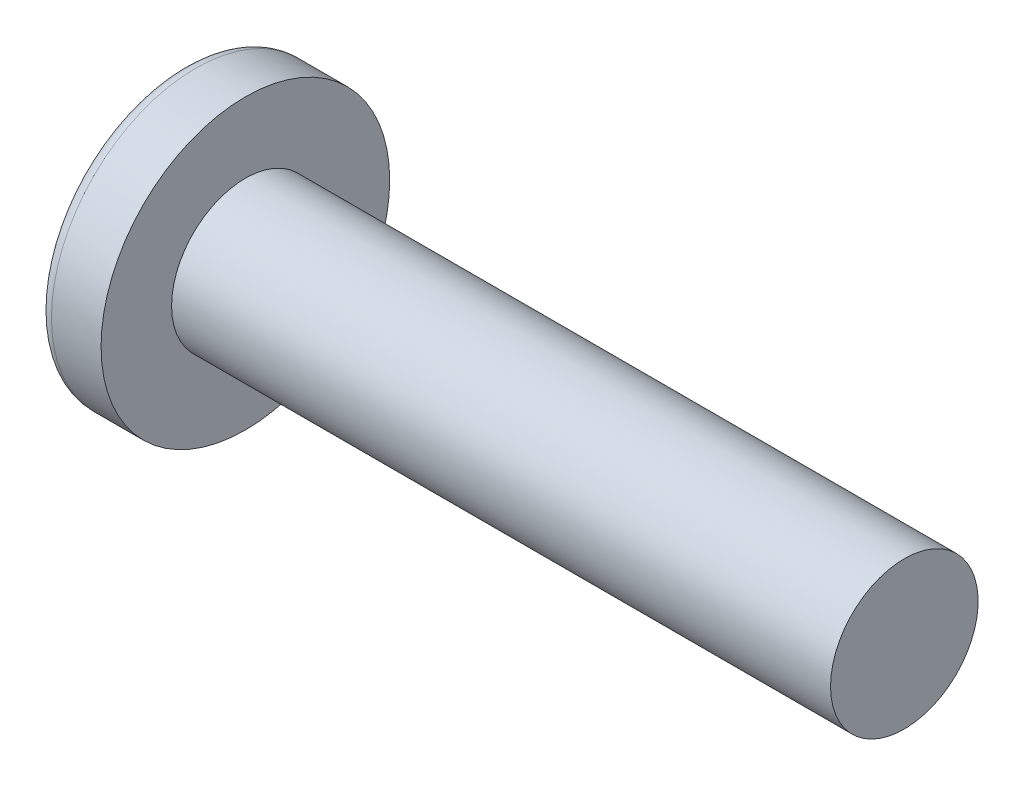
SolidWorks part; units mm, degrees
ref_plane "Plane1" through (0, 0, 0) normal (0, 0, 1) x (1, 0, 0)
ref_plane "Plane2" through (0, 0, 0) normal (0, 1, 0) x (1, 0, 0)
ref_plane "Plane3" through (0, 0, 0) normal (1, 0, 0) x (0, 0, -1)
sketch "BodySke" plane through (0, 0, 0) normal (0, 0, 1) x (1, 0, 0)
  line L0 (2.032, 1.4224) -> (2.032, 2.7813)
  line L1 (2.3495, 6.35) -> (2.3495, -3.175) construction
  line L2 (-25.4, 0) -> (127, 0) construction
  line L3 (14.732, 0) -> (0, 0)
  line L4 (2.032, 1.4224) -> (14.732, 1.4224)
  line L5 (14.732, 1.4224) -> (14.732, 0)
  line L6 (1.0756, 2.7813) -> (2.032, 2.7813)
  line L7 (2.032, -1.4224) -> (14.732, -1.4224) construction
  line L8 (2.032, 6.35) -> (2.032, -3.175) construction
  arc A0 (0.8702, 2.6767) -> (0, 0) centre (4.5517, 0) ccw
  arc A2 (0.8702, 2.6767) -> (1.0756, 2.7813) centre (1.0756, 2.5273) cw
  dimension "Head_fillet_rad" = 0.254
  dimension "Head_crown_rad" = 4.5517
  dimension "Head_ht" = 2.032
  dimension "Diameter" = 2.8448
  dimension "Length" = 12.7
  dimension "Head_dia" = 5.5626
  dimension "Advance" = 0.635
  dimension "Thread_nom" = 12.7
revolve "Base-Revolve" add sketch "BodySke" angle 360 about L2
cosmetic thread "ThreadCosmetic" [suppressed] parameters "Thread_length"=12.065, "Thread_minor"=2.0879
sketch "Sketch3" plane through (0, 0, 0) normal (1, 0, 0) x (0, 0, -1)
  line L0 (0.4064, -1.8161) -> (-0.4064, -1.8161)
  line L1 (0.4064, -1.8161) -> (0.4064, 1.8161)
  line L2 (-0.4064, 1.8161) -> (0.4064, 1.8161)
  line L3 (-0.4064, 1.8161) -> (-0.4064, -1.8161)
  dimension "D1" = 1.8161
  dimension "Cross_dia" = 3.6322
  dimension "D2" = 0.4064
  dimension "Cross_width" = 0.8128
ref_plane "Plane4" through (2.0066, 0, 0) normal (1, 0, 0) x (0, 0, -1)
sketch "Sketch4" plane through (2.0066, 0, 0) normal (1, 0, 0) x (0, 0, -1)
  line L0 (0.2032, -0.2032) -> (-0.2032, -0.2032)
  line L1 (0.2032, -0.2032) -> (0.2032, 0.2032)
  line L2 (-0.2032, 0.2032) -> (0.2032, 0.2032)
  line L3 (-0.2032, 0.2032) -> (-0.2032, -0.2032)
  dimension "D1" = 0.4064
  dimension "D2" = 0.4064
  dimension "D3" = 0.2032
  dimension "D4" = 0.2032
loft "Cut-Loft1" cut profiles "Sketch3", "Sketch4"
pattern_circular "CirPattern1" count 2 every 90 about axis through (0, 0, 0) along (1, 0, 0) of "Cut-Loft1"
sketch "ThdSchSke" plane through (0, 0, 0) normal (0, 0, 1) x (1, 0, 0)
  line L0 (2.667, -1.0439) -> (2.402, -1.4224)
  line L1 (2.667, -1.0439) -> (2.932, -1.4224)
  line L2 (2.932, -1.4224) -> (2.932, -1.778)
  line L3 (-3.175, 0) -> (5.1513, 0) construction
  line L5 (2.932, -1.778) -> (2.402, -1.778)
  line L6 (2.402, -1.778) -> (2.402, -1.4224)
  dimension "Thread_minor" = 2.0879
  dimension "Diameter" = 2.8448
  dimension "Start" = 2.667
  dimension "SideAngle" = 55
  dimension "VeeAngle" = 70
  dimension "Overcut" = 3.556
revolve "ThreadSchematic" [suppressed] cut sketch "ThdSchSke" angle 360 about L3
pattern_linear "ThdSchPat" [suppressed]
equation "\"D1@Sketch3\" = \"Cross_dia@Sketch3\" / 2"
equation "\"D2@Sketch3\" = \"Cross_width@Sketch3\" / 2"
equation "\"D1@Sketch4\" = \"Cross_width@Sketch3\" *.5"
equation "\"D2@Sketch4\" = \"D1@Sketch4\""
equation "\"D3@Sketch4\" = \"D1@Sketch4\" / 2"
equation "\"D4@Sketch4\" = \"D2@Sketch4\" / 2"
equation "\"Thread_length@ThreadCosmetic\" = ((sgn( (\"Length@BodySke\" - \"Advance@BodySke\" ) - \"Thread_nom@BodySke\" )-1)*( (\"Length@BodySke\" - \"Advance@BodySke\" ) - \"Thread_nom@BodySke\" ))/-2+ \"Thread_nom@BodySke\""
equation "\"Thread_minor@ThdSchSke\" = \"Thread_minor@ThreadCosmetic\""
equation "\"Diameter@ThdSchSke\" = \"Diameter@BodySke\""
equation "\"Overcut@ThdSchSke\" = \"Diameter@BodySke\" * 1.25"
equation "\"Start@ThdSchSke\" = \"Head_ht@BodySke\" + \"Length@BodySke\" - \"Thread_length@ThreadCosmetic\"  '---Non-countersunk---"
equation "\"Num_threads@ThdSchPat\" = int( \"Thread_length@ThreadCosmetic\" / \"Advance@BodySke\" + 0.999 )  + 1"
equation "\"Advance@ThdSchPat\" = \"Thread_length@ThreadCosmetic\" /  (\"Num_threads@ThdSchPat\" - 1) 'relax it"
